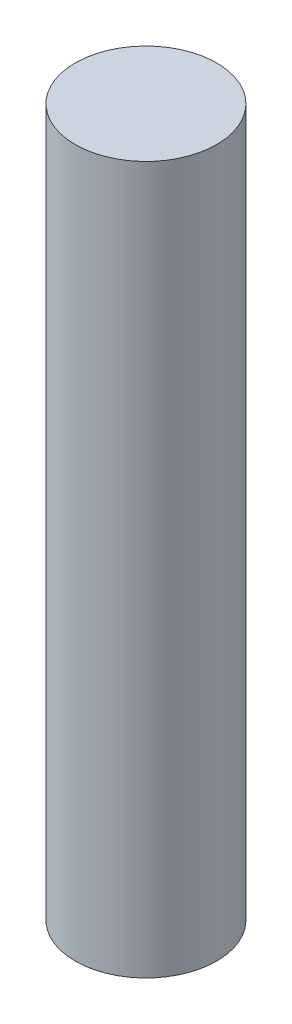
SolidWorks part; units mm, degrees
ref_plane "前视基准面" through (0, 0, 0) normal (0, 0, 1) x (1, 0, 0)
ref_plane "上视基准面" through (0, 0, 0) normal (0, 1, 0) x (1, 0, 0)
ref_plane "右视基准面" through (0, 0, 0) normal (1, 0, 0) x (0, 0, -1)
sketch "草图1" plane through (0, 0, 0) normal (0, 1, 0) x (1, 0, 0)
  circle A0 centre (0, 0) radius 5
  dimension "D1" = 10
extrude "凸台-拉伸1" add sketch "草图1" along normal blind 50
